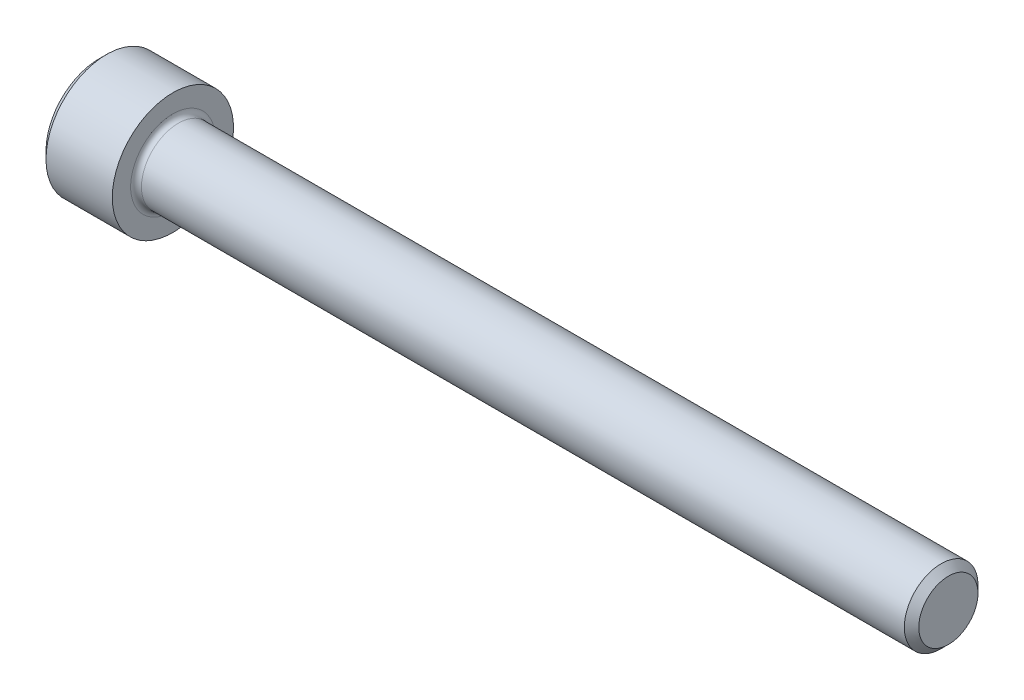
SolidWorks part; units mm, degrees
revolve "Base-Revolve" add sketch "BodySke"
sketch "BodySke" plane through (0, 0, 0) normal (0, 0, 1) x (1, 0, 0)
  line L0 (0, 0) -> (0, 3.4861)
  line L1 (0.4826, 3.9688) -> (4.826, 3.9688)
  line L2 (4.826, 3.9688) -> (4.826, 2.413)
  line L3 (4.826, 2.413) -> (55.1536, 2.413)
  line L4 (55.626, 1.9406) -> (55.626, 0)
  line L5 (55.626, 0) -> (0, 0)
  line L6 (-31.75, 0) -> (127, 0) construction
  line L7 (0, 3.4861) -> (0.4826, 3.9688)
  line L8 (55.626, 1.9406) -> (55.1536, 2.413)
  line L9 (0, -3.4861) -> (0.4826, -3.9688) construction
  line L10 (55.626, -1.9406) -> (55.1536, -2.413) construction
  line L11 (5.6185, 9.525) -> (5.6185, 3.175) construction
  line L12 (27.051, 9.525) -> (27.051, 3.175) construction
  line L13 (17.526, 9.525) -> (17.526, 3.175) construction
  dimension "Diameter" = 4.826
  dimension "Head_ht" = 4.826
  dimension "Length" = 50.8
  dimension "Body_ch_ang" = 45
  dimension "Head_dia" = 7.9375
  dimension "Head_ch_ang" = 45
  dimension "Head_side_ht" = 4.3434
  dimension "Minor_dia" = 3.8811
  dimension "Advance" = 0.7925
  dimension "Thread_nom" = 28.575
  dimension "Thread_length" = 38.1
cosmetic thread "ThreadCosmetic" [suppressed]
fillet "Fillet1" radius 0.3556 1 edges at (4.826, 0, 2.413)
ref_plane "Plane1" through (0, 0, 0) normal (0, 0, 1) x (1, 0, 0)
ref_plane "Plane2" through (0, 0, 0) normal (0, 1, 0) x (1, 0, 0)
ref_plane "Plane3" through (0, 0, 0) normal (1, 0, 0) x (0, 0, -1)
sketch "Sketch2" plane through (0, 0, 0) normal (0, 0, 1) x (1, 0, 0)
  line L0 (0, 1.985) -> (2.286, 1.985)
  line L1 (2.286, 1.985) -> (3.432, 0)
  line L2 (-31.75, 0) -> (127, 0) construction
  line L3 (3.432, 0) -> (0, 0)
  line L4 (0, 0) -> (0, 1.985)
  line L5 (0, 3.4861) -> (0, -3.4861) construction
  line L6 (0, 0) -> (47.625, 0) construction
  line L7 (4.826, -3.9688) -> (4.826, 3.9688) construction
  dimension "D1" = 1.985
  dimension "D2" = 60
revolve "Hex-PreBroach" cut sketch "Sketch2" angle 360 about L6
sketch "Sketch3" plane through (0, 0, 0) normal (-1, 0, 0) x (0, 0.5, 0.866)
  line L0 (1.146, 1.985) -> (-1.146, 1.985)
  line L1 (-1.146, 1.985) -> (-2.2921, 0)
  line L2 (1.146, 1.985) -> (2.2921, 0)
  line L3 (1.146, -1.985) -> (2.2921, 0)
  line L4 (1.146, -1.985) -> (-1.146, -1.985)
  line L5 (-1.146, -1.985) -> (-2.2921, 0)
  dimension "D1" = 1.985
  dimension "D2" = 1.985
  dimension "Hex_size" = 3.97
extrude "Hex" cut sketch "Sketch3" against normal blind 2.286
sketch "Sketch4" plane through (0, 0, 0) normal (-1, 0, 0) x (0, 0, 1)
  line L0 (0, 0) -> (2.3876, 0)
  line L1 (0, 0) -> (6.1484, 3.5498) construction
  line L2 (0, 0) -> (1.1938, 2.0677)
  line L3 (1.9883, 0.576) -> (2.2704, 0.7389)
  line L4 (1.493, 1.4339) -> (1.7751, 1.5968)
  arc A0 (1.9883, 0.576) -> (1.493, 1.4339) centre (0, 0) ccw
  arc A1 (2.3876, 0) -> (2.2704, 0.7389) centre (0, 0) ccw
  arc A2 (1.1938, 2.0677) -> (1.7751, 1.5968) centre (0, 0) cw
  dimension "D1" = 30
  dimension "D2" = 60
  dimension "Spline_p_dim" = 0.9906
  dimension "D3" = 0.4953
extrude "Spline" [suppressed] cut sketch "Sketch4" against normal blind 2.286
pattern_circular "CirPattern1" [suppressed] count 6 every 60
sketch "Sketch5" plane through (0, 0, 0) normal (0, 0, 1) x (1, 0, 0)
  line L0 (-31.75, 0) -> (127, 0) construction
  line L2 (0, 3.4861) -> (0, -3.4861) construction
  circle A0 centre (1.651, 0) radius 0.5906
  dimension "Drilled_hole_dia" = 1.1811
  dimension "Drilled_hole_loc" = 1.651
extrude "Hole" [suppressed] cut sketch "Sketch5" against normal through all and the other way through all
pattern_circular "Drilled-4" [suppressed] count 2 every 60
pattern_circular "Drilled-6" [suppressed] count 3 every 60
sketch "ThdSchSke" plane through (0, 0, 0) normal (0, 0, 1) x (1, 0, 0)
  line L0 (27.051, -1.9406) -> (26.7202, -2.413)
  line L1 (27.051, -1.9406) -> (27.3818, -2.413)
  line L2 (27.3818, -2.413) -> (27.3818, -3.0162)
  line L3 (-3.175, 0) -> (5.1513, 0) construction
  line L5 (27.3818, -3.0162) -> (26.7202, -3.0162)
  line L6 (26.7202, -3.0162) -> (26.7202, -2.413)
  line L7 (0, 3.4861) -> (0, -3.4861) construction
  dimension "Thread_minor" = 3.8811
  dimension "Diameter" = 4.826
revolve "ThreadSchematic" [suppressed] cut sketch "ThdSchSke" angle 360 about L3
pattern_linear "ThdSchPat" [suppressed]
equation "\"D2@Sketch3\" = \"Hex_size@Sketch3\" / 2"
equation "\"D1@Sketch3\" = \"Hex_size@Sketch3\" / 2"
equation "\"D1@Sketch2\" = \"Hex_size@Sketch3\" / 2"
equation "\"D3@Sketch4\" = \"Spline_p_dim@Sketch4\" / 2"
equation "\"Thread_minor@ThreadCosmetic\"  =  \"Minor_dia@BodySke\""
equation "\"D2@CirPattern1\" = 360 / \"Num_teeth@CirPattern1\""
equation "\"Wall_thickness@Sketch2\" = \"Head_ht@BodySke\" - \"Key_eng@Hex\""
equation "\"Thread_length@ThreadCosmetic\" = ((sgn( (\"Length@BodySke\" - \"Advance@BodySke\" ) - \"Thread_nom@BodySke\" )-1)*( (\"Length@BodySke\" - \"Advance@BodySke\" ) - \"Thread_nom@BodySke\" ))/-2+ \"Thread_nom@BodySke\""
equation "\"Thread_minor@ThdSchSke\" = \"Minor_dia@BodySke\""
equation "\"Diameter@ThdSchSke\" = \"Diameter@BodySke\""
equation "\"Overcut@ThdSchSke\" = \"Diameter@BodySke\" * 1.25"
equation "\"Start@ThdSchSke\" = \"Head_ht@BodySke\" + \"Length@BodySke\" - \"Thread_length@ThreadCosmetic\"  '---Non-countersunk---"
equation "\"Num_threads@ThdSchPat\" = int( \"Thread_length@ThreadCosmetic\" / \"Advance@BodySke\" + 0.999 )  + 1"
equation "\"Advance@ThdSchPat\" = \"Thread_length@ThreadCosmetic\" /  (\"Num_threads@ThdSchPat\" - 1) 'relax it"
equation "\"Num_threads@ThdSchPat\" = \"Num_threads@ThdSchPat\" - sgn( \"Num_threads@ThdSchPat\" - 1) '---chamfered tips only---"
